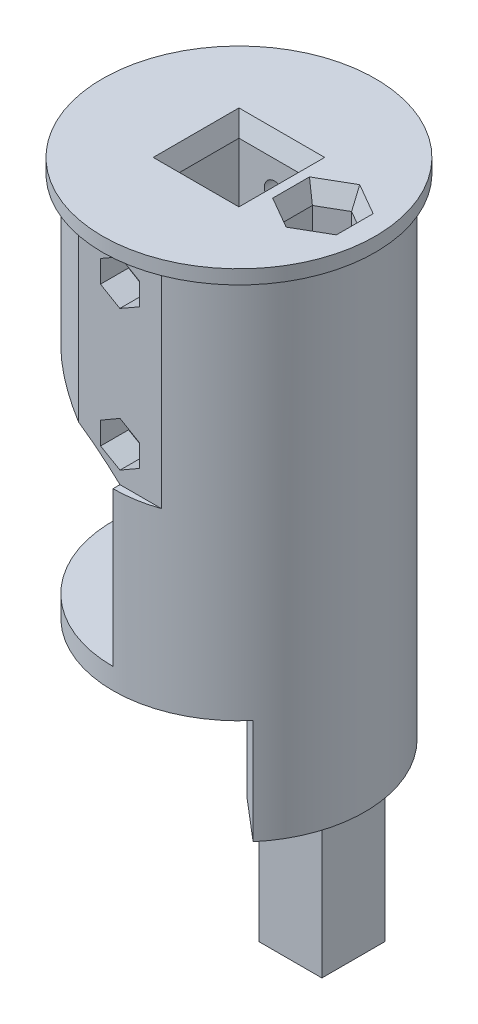
SolidWorks part; units mm, degrees
ref_plane "Спереди" through (0, 0, 0) normal (0, 0, 1) x (1, 0, 0)
ref_plane "Сверху" through (0, 0, 0) normal (0, 1, 0) x (1, 0, 0)
ref_plane "Справа" through (0, 0, 0) normal (1, 0, 0) x (0, 0, -1)
sketch "Эскиз1" plane through (0, 0, 0) normal (0, 1, 0) x (1, 0, 0)
  circle A0 centre (0, 0) radius 18
  dimension "D1" = 36
extrude "Бобышка-Вытянуть1" add sketch "Эскиз1" along normal blind 55
sketch "Эскиз2" plane through (0, 55, 0) normal (0, 1, 0) x (1, 0, 0)
  circle A0 centre (0, 0) radius 19.5
  dimension "D1" = 39
extrude "Бобышка-Вытянуть2" add sketch "Эскиз2" along normal blind 2
sketch "Эскиз3" plane through (0, 57, 0) normal (0, 1, 0) x (1, 0, 0)
  line L1 (-5.125, -5.125) -> (5.125, -5.125)
  line L2 (-5.125, -5.125) -> (-5.125, 5.125)
  line L3 (-5.125, 5.125) -> (5.125, 5.125)
  line L4 (5.125, -5.125) -> (5.125, 5.125)
  line L5 (-5.125, -5.125) -> (5.125, 5.125) construction
  line L6 (-5.125, 5.125) -> (5.125, -5.125) construction
  point P0 (0, 0)
  dimension "D1" = 10.25
extrude "Вырез-Вытянуть1" cut sketch "Эскиз3" against normal blind 40
sketch "Эскиз4" plane through (0, 0, 0) normal (0, -1, 0) x (1, 0, 0)
  line L0 (0, 0) -> (11.5702, 13.7888) construction
  line L1 (0, 0) -> (11.5702, -13.7888) construction
  line L2 (11.5702, 13.7888) -> (11.5702, -13.7888) construction
  line L3 (0, 0) -> (13.6996, 11.6756) construction
  line L5 (5.1423, -6.1284) -> (11.5702, -13.7888)
  line L6 (5.1423, -6.1284) -> (5.1423, 4.3826)
  line L7 (5.1423, 4.3826) -> (13.6996, 11.6756)
  circle A3 centre (0, 0) radius 18 construction
  arc A4 (13.6996, 11.6756) -> (11.5702, -13.7888) centre (0, 0) cw
  point P5 (11.5702, 13.7888)
  point P8 (11.5702, -13.7888)
  dimension "D1" = 100
  dimension "D2" = 3
  dimension "D3" = 10
extrude "Бобышка-Вытянуть3" add sketch "Эскиз4" along normal blind 15
sketch "Sketch1" plane through (0, -15, 0) normal (0, -1, 0) x (1, 0, 0)
  circle A0 centre (0, 0) radius 18
  arc A3 (13.6996, 11.6756) -> (11.5702, -13.7888) centre (0, 0) ccw construction
extrude "Boss-Extrude1" add sketch "Sketch1" along normal blind 20
sketch "Sketch3" plane through (0, -35, 0) normal (0, -1, 0) x (1, 0, 0)
  circle A0 centre (0, 0) radius 18
  circle A3 centre (0, 0) radius 18 construction
extrude "Boss-Extrude2" add sketch "Sketch3" along normal blind 7
sketch "Sketch4" plane through (0, -42, 0) normal (0, -1, 0) x (1, 0, 0)
  line L1 (5.1, 5.1) -> (-5.1, 5.1)
  line L2 (5.1, 5.1) -> (5.1, -5.1)
  line L3 (5.1, -5.1) -> (-5.1, -5.1)
  line L4 (-5.1, 5.1) -> (-5.1, -5.1)
  line L5 (5.1, 5.1) -> (-5.1, -5.1) construction
  line L6 (5.1, -5.1) -> (-5.1, 5.1) construction
  point P0 (0, 0)
  dimension "D1" = 10.2
  dimension "D2" = 10.2
extrude "Cut-Extrude2" cut sketch "Sketch4" against normal blind 27
sketch "Sketch6" plane through (0, 0, 0) normal (0, -1, 0) x (1, 0, 0)
  line L0 (0, 18) -> (0, -18) construction
  line L1 (0, 18) -> (0, -18)
  arc A0 (13.6996, 11.6756) -> (11.5702, -13.7888) centre (0, 0) ccw construction
  arc A1 (0, -18) -> (0, 18) centre (0, 0) cw
extrude "Cut-Extrude4" cut sketch "Sketch6" against normal blind 25
sketch "Sketch8" plane through (0, 0, 0) normal (0, -1, 0) x (1, 0, 0)
  line L0 (0, -18) -> (0, 18)
  arc A0 (0, -18) -> (0, 18) centre (0, 0) cw
  arc A1 (13.6996, 11.6756) -> (0, 18) centre (0, 0) ccw construction
extrude "Boss-Extrude3" add sketch "Sketch8" against normal blind 3
sketch "Sketch9" plane through (0, 0, 0) normal (-1, 0, 0) x (0, 0, 1)
  line L0 (-18, 3) -> (18, 25) construction
  line L2 (18, 25) -> (-18, 25)
  line L3 (18, 25) -> (18, 3)
  line L4 (18, 3) -> (-18, 3)
  line L5 (-18, 25) -> (-18, 3)
  line L6 (18, 25) -> (-18, 3) construction
  line L7 (18, 3) -> (-18, 25) construction
  point P4 (0, 14)
extrude "Cut-Extrude5" cut sketch "Sketch9" against normal blind 8
sketch "Sketch10" plane through (0, 0, 0) normal (0, -1, 0) x (1, 0, 0)
  line L0 (0, -18) -> (0, 18) construction
  line L2 (1.5, 8.7) -> (-1.5, 8.7)
  line L3 (1.5, 8.7) -> (1.5, 6.7)
  line L4 (1.5, 6.7) -> (-1.5, 6.7)
  line L5 (-1.5, 8.7) -> (-1.5, 6.7)
  line L6 (1.5, 8.7) -> (-1.5, 6.7) construction
  line L7 (1.5, 6.7) -> (-1.5, 8.7) construction
  circle A0 centre (0, 0) radius 3.7
  arc A1 (13.6996, 11.6756) -> (11.5702, -13.7888) centre (0, 0) ccw construction
  point P9 (0, 7.7)
  point P14 (0, 3.7)
  dimension "D1" = 7.4
  dimension "D2" = 2
  dimension "D3" = 3
  dimension "D4" = 4
extrude "Cut-Extrude6" cut sketch "Sketch10" against normal blind 10
sketch "Sketch11" plane through (0, -42, 0) normal (0, -1, 0) x (1, 0, 0)
  line L0 (-18, 0) -> (18, 0) construction
  circle A0 centre (0, 0) radius 18 construction
  circle A1 centre (12, 0) radius 2
  dimension "D1" = 4
  dimension "D2" = 6
extrude "Cut-Extrude7" cut sketch "Sketch11" against normal blind 102
sketch "Sketch15" plane through (0, -42, 0) normal (0, -1, 0) x (1, 0, 0)
  circle A0 centre (0, 0) radius 18
  circle A3 centre (0, 0) radius 18 construction
extrude "Cut-Extrude9" cut sketch "Sketch15" against normal blind 27
sketch "Sketch17" plane through (0, 25, 0) normal (0, -1, 0) x (1, 0, 0)
  line L2 (-18, 0) -> (14.8, 0) construction
  line L3 (14.8, 0) -> (13.8, 0) construction
  line L4 (0, 18) -> (0, -18) construction
  line L6 (5.9161, -17) -> (-5.9161, -17)
  line L7 (5.9161, 17) -> (-5.9161, 17)
  arc A0 (8, 16.1245) -> (8, -16.1245) centre (0, 0) ccw construction
  arc A1 (-5.9161, -17) -> (5.9161, -17) centre (0, 0) ccw
  arc A2 (-5.9161, 17) -> (5.9161, 17) centre (0, 0) cw
  point P14 (13.8, 0)
  point P20 (0, -17)
  point P23 (0, 17)
  dimension "D4" = 1
extrude "Cut-Extrude11" cut sketch "Sketch17" against normal blind 30
sketch "Sketch18" plane through (0, 0, -17) normal (0, 0, 1) x (1, 0, 0)
  line L0 (0, 25) -> (0, 55) construction
  line L1 (5.9161, 25) -> (-5.9161, 25) construction
  line L2 (5.9161, 55) -> (-5.9161, 55) construction
  circle A0 centre (0, 30) radius 1.5
  circle A1 centre (0, 50) radius 1.5
  point P3 (0, 40)
  dimension "D1" = 3
  dimension "D2" = 10
  dimension "D3" = 20
extrude "Cut-Extrude12" cut sketch "Sketch18" along normal through all
sketch "Sketch19" plane through (0, 0, -17) normal (0, 0, 1) x (1, 0, 0)
  circle A0 centre (0, 30) radius 3
  circle A1 centre (0, 50) radius 3
  dimension "D1" = 6
extrude "Cut-Extrude13" cut sketch "Sketch19" along normal blind 3
sketch "Sketch23" plane through (0, 3, 0) normal (0, 1, 0) x (1, 0, 0)
  line L0 (0, 18) -> (0, -18) construction
  line L1 (0, -14.4) -> (8, -14.4)
  line L2 (8, 16.1245) -> (8, -16.1245) construction
  line L3 (0, 14.4) -> (8, 14.4)
  line L4 (0, -14.4) -> (0, -18)
  line L5 (0, 14.4) -> (0, 18)
  line L6 (8, -14.4) -> (8, -16.1245)
  line L7 (8, 16.1245) -> (8, 14.4)
  arc A0 (8, 16.1245) -> (8, -16.1245) centre (0, 0) ccw construction
  arc A1 (0, -18) -> (8, -16.1245) centre (0, 0) ccw
  arc A2 (0, 18) -> (8, 16.1245) centre (0, 0) cw
  arc A3 (-5.9161, 17) -> (-5.9161, -17) centre (0, 0) ccw construction
  arc A4 (11.5702, 13.7888) -> (13.6996, -11.6756) centre (0, 0) ccw construction
  dimension "D1" = 3.6
extrude "Boss-Extrude5" add sketch "Sketch23" along normal blind 22
sketch "Sketch25" plane through (0, 0, 17) normal (0, 0, 1) x (1, 0, 0)
  line L0 (0, 55) -> (0, 25) construction
  line L1 (2.7713, 28.4) -> (2.7713, 31.6)
  line L2 (2.7713, 31.6) -> (0, 33.2)
  line L3 (0, 33.2) -> (-2.7713, 31.6)
  line L4 (-2.7713, 31.6) -> (-2.7713, 28.4)
  line L5 (-2.7713, 28.4) -> (0, 26.8)
  line L6 (0, 26.8) -> (2.7713, 28.4)
  line L7 (-5.9161, 55) -> (5.9161, 55) construction
  line L9 (-2.7821, 48.4189) -> (-0.0218, 46.8001)
  line L10 (-0.0218, 46.8001) -> (2.7603, 48.3811)
  line L11 (2.7603, 48.3811) -> (2.7821, 51.5811)
  line L12 (2.7821, 51.5811) -> (0.0218, 53.1999)
  line L13 (0.0218, 53.1999) -> (-2.7603, 51.6189)
  line L14 (-2.7603, 51.6189) -> (-2.7821, 48.4189)
  circle A0 centre (0, 30) radius 3.2 construction
  circle A1 centre (0, 50) radius 3.2 construction
  point P24 (0, 40)
  dimension "D1" = 6.4
  dimension "D2" = 20
  dimension "D3" = 10
extrude "Cut-Extrude16" cut sketch "Sketch25" against normal blind 4
sketch "Sketch26" plane through (0, 57, 0) normal (0, 1, 0) x (1, 0, 0)
  line L0 (14.8, 0) -> (5.125, 0) construction
  line L2 (8.4493, -2.05) -> (12, -4.1)
  line L3 (12, -4.1) -> (15.5507, -2.05)
  line L4 (15.5507, -2.05) -> (15.5507, 2.05)
  line L5 (15.5507, 2.05) -> (12, 4.1)
  line L6 (12, 4.1) -> (8.4493, 2.05)
  line L7 (5.125, -5.125) -> (5.125, 5.125) construction
  line L8 (8.4493, 2.05) -> (8.4493, -2.05)
  circle A0 centre (12, 0) radius 4.1 construction
  point P2 (15.5507, 0)
  dimension "D1" = 8.2
extrude "Cut-Extrude17" cut sketch "Sketch26" against normal blind 25.4
sketch "Sketch27" plane through (0, 0, 17) normal (0, 0, 1) x (1, 0, 0)
  line L0 (0, 25) -> (-20, 36.547) construction
  line L1 (-20, 36.547) -> (-20, 25)
  line L2 (-20, 25) -> (0, 25)
  line L3 (-18, 25) -> (-5.9161, 25) construction
  line L4 (-5.9161, 25) -> (0, 25) construction
  arc A0 (0, 25) -> (-20, 36.547) centre (-34.3242, -11.3572) ccw
  dimension "D3" = 50
  dimension "D1" = 30
  dimension "D2" = 20
extrude "Cut-Extrude18" cut sketch "Sketch27" against normal through all
fillet "Fillet2" radius 5 2 edges at (8, 14, 14.4) (8, 14, -14.4)
sketch "Sketch30" plane through (8, 0, 0) normal (-1, 0, 0) x (0, 0, 1)
  line L0 (-9.4, 8) -> (9.4, 8) construction
  line L1 (-9.4, 25) -> (-9.4, 3) construction
  line L2 (9.4, 3) -> (9.4, 25) construction
  line L4 (9.4, 13) -> (-9.4, 13)
  line L5 (9.4, 13) -> (9.4, 3)
  line L6 (9.4, 3) -> (-9.4, 3)
  line L7 (-9.4, 13) -> (-9.4, 3)
  line L8 (9.4, 13) -> (-9.4, 3) construction
  line L9 (9.4, 3) -> (-9.4, 13) construction
  point P6 (0, 8)
  dimension "D1" = 10
extrude "Cut-Extrude20" cut sketch "Sketch30" against normal blind 3
chamfer "Chamfer1" distance 1 angle 70 4 edges at (5.125, 57, 0) (0, 57, 5.125) (-5.125, 57, 0) (0, 57, -5.125)
chamfer "Chamfer2" distance 1 angle 70 6 edges at (15.5507, 57, 0) (13.7754, 57, 3.075) (13.7754, 57, -3.075) (10.2246, 57, -3.075) (8.4493, 57, 0) (10.2246, 57, 3.075)
sketch "Sketch37" plane through (0, -15, 0) normal (0, -1, 0) x (1, 0, 0)
  line L0 (5.1423, -0.8729) -> (17.9788, -0.8729) construction
  line L1 (5.1423, 4.3826) -> (5.1423, -6.1284) construction
  line L3 (15.4788, 3.6271) -> (6.4788, 3.6271)
  line L4 (15.4788, 3.6271) -> (15.4788, -5.3729)
  line L5 (15.4788, -5.3729) -> (6.4788, -5.3729)
  line L6 (6.4788, 3.6271) -> (6.4788, -5.3729)
  line L7 (15.4788, 3.6271) -> (6.4788, -5.3729) construction
  line L8 (15.4788, -5.3729) -> (6.4788, 3.6271) construction
  arc A0 (11.5702, -13.7888) -> (13.6996, 11.6756) centre (0, 0) ccw construction
  circle A1 centre (12, 0) radius 2
  point P8 (10.9788, -0.8729)
  dimension "D1" = 9
  dimension "D2" = 7
extrude "Boss-Extrude7" add sketch "Sketch37" along normal blind 20
sketch "Sketch38" plane through (0, -15, 0) normal (0, -1, 0) x (1, 0, 0)
  line L0 (5.1423, -6.1284) -> (5.1423, 4.3826)
  arc A0 (5.1423, -6.1284) -> (5.1423, 4.3826) centre (-10.9482, -0.8729) ccw
extrude "Cut-Extrude22" cut sketch "Sketch38" against normal up to surface (15 mm away) up to face at (0, 0, 7.7)
sketch "Sketch39" plane through (0, -15, 0) normal (0, -1, 0) x (1, 0, 0)
  line L0 (7.4207, -7.3729) -> (15.4207, -7.3729)
  line L1 (7.4207, -7.3729) -> (11.5989, -12.3522)
  line L2 (5.1423, -6.1284) -> (11.5702, -13.7888) construction
  line L3 (6.4788, -5.3729) -> (15.4788, -5.3729) construction
  line L4 (6.1866, -7.3729) -> (16.4207, -7.3729) construction
  arc A0 (11.5989, -12.3522) -> (15.4207, -7.3729) centre (-0.5503, 0.9293) ccw
  arc A1 (11.5702, -13.7888) -> (13.6996, 11.6756) centre (0, 0) ccw construction
  point P11 (11.4207, -7.3729)
  dimension "D1" = 8
  dimension "D2" = 2
  dimension "D3" = 6.5
  dimension "D4" = 5
  dimension "D6" = 50
extrude "Cut-Extrude23" cut sketch "Sketch39" against normal up to surface (28 mm away) up to face at (9.8333, 13, 0)
sketch "Sketch40" plane through (0, 3, 0) normal (0, 1, 0) x (1, 0, 0)
  line L0 (7.4207, 7.3729) -> (7.4207, 11.736)
  line L1 (7.4207, 11.736) -> (11.7839, 11.736)
  line L2 (11.7839, 11.736) -> (11.7839, 7.3729)
  line L3 (11.7839, 7.3729) -> (7.4207, 7.3729)
  line L4 (7.4207, 7.3729) -> (11, 7.3729) construction
  arc A1 (8, 9.4) -> (3, 14.4) centre (3, 9.4) ccw construction
extrude "Cut-Extrude24" cut sketch "Sketch40" along normal up to surface (10 mm away) up to face at (10.5956, 13, -3.0295)
fillet "Fillet7" radius 6 2 edges at (5.1423, -7.5, 4.3826) (5.1423, -7.5, -6.1284)
